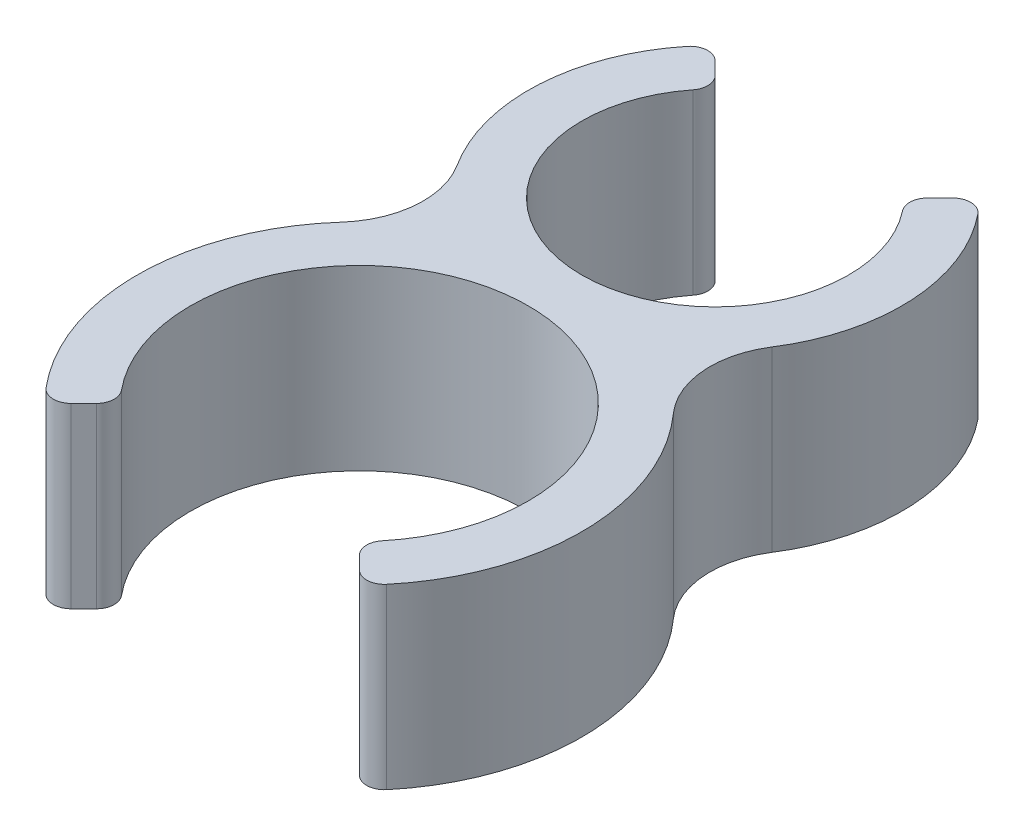
SolidWorks part; units mm, degrees
ref_plane "Front Plane" through (0, 0, 0) normal (0, 0, 1) x (1, 0, 0)
ref_plane "Top Plane" through (0, 0, 0) normal (0, 1, 0) x (1, 0, 0)
ref_plane "Right Plane" through (0, 0, 0) normal (1, 0, 0) x (0, 0, -1)
sketch "Sketch1" plane through (0, 0, 0) normal (0, 1, 0) x (1, 0, 0)
  line L0 (0, -10) -> (0, 10) construction
  line L1 (0, 10) -> (0, 20.5) construction
  line L2 (0, -10) -> (0, -22.5) construction
  line L3 (-5.3033, 15.3033) -> (-7.4246, 17.4246)
  line L4 (-6.7175, -16.7175) -> (-8.8388, -18.8388)
  line L5 (5.3033, 15.3033) -> (7.4246, 17.4246)
  line L6 (6.7175, -16.7175) -> (8.8388, -18.8388)
  arc A0 (-5.3033, 15.3033) -> (5.3033, 15.3033) centre (0, 10) ccw
  arc A1 (6.7175, -16.7175) -> (-6.7175, -16.7175) centre (0, -10) ccw
  arc A2 (-7.4246, 17.4246) -> (-5.6504, 1.15) centre (0, 10) ccw
  arc A3 (8.8388, -18.8388) -> (5.6504, 1.15) centre (0, -10) ccw
  arc A4 (-5.6504, 1.15) -> (-8.8388, -18.8388) centre (0, -10) ccw
  arc A5 (5.6504, 1.15) -> (7.4246, 17.4246) centre (0, 10) ccw
  point P4 (0, 0)
  point P8 (0, 0)
  dimension "D1" = 19
  dimension "D2" = 15
  dimension "D4" = 3
  dimension "D5" = 3
  dimension "D3" = 20
  dimension "D6" = 45
  dimension "D7" = 45
extrude "Boss-Extrude1" add sketch "Sketch1" along normal blind 10
fillet "Fillet1" radius 1 8 edges at (8.8388, 5, 18.8388) (6.7175, 5, 16.7175) (-8.8388, 5, 18.8388) (-6.7175, 5, 16.7175) (-5.3033, 5, -15.3033) (7.4246, 5, -17.4246) (5.3033, 5, -15.3033) (-7.4246, 5, -17.4246)
fillet "Fillet2" radius 5 2 edges at (5.6504, 5, -1.15) (-5.6504, 5, -1.15)
